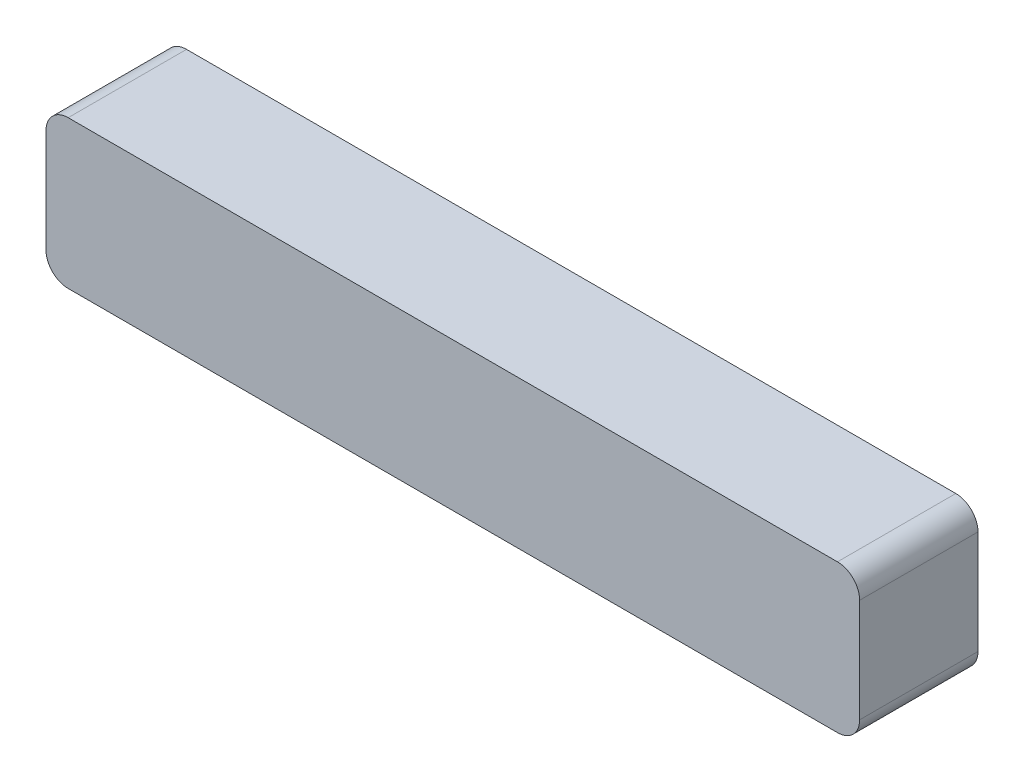
SolidWorks part; units mm, degrees
ref_plane "前视基准面" through (0, 0, 0) normal (0, 0, 1) x (1, 0, 0)
ref_plane "上视基准面" through (0, 0, 0) normal (0, 1, 0) x (1, 0, 0)
ref_plane "右视基准面" through (0, 0, 0) normal (1, 0, 0) x (0, 0, -1)
sketch "草图1" plane through (0, 0, 0) normal (0, 0, 1) x (1, 0, 0)
  line L1 (3, 0) -> (107, 0)
  line L2 (0, 3) -> (0, 17)
  line L3 (3, 20) -> (107, 20)
  line L4 (110, 3) -> (110, 17)
  arc A0 (110, 3) -> (107, 0) centre (107, 3) cw
  arc A1 (110, 17) -> (107, 20) centre (107, 17) ccw
  arc A2 (0, 3) -> (3, 0) centre (3, 3) ccw
  arc A3 (0, 17) -> (3, 20) centre (3, 17) cw
  point P7 (110, 0)
  point P12 (0, 0)
  point P15 (0, 20)
  dimension "D3" = 3
  dimension "D1" = 20
  dimension "D2" = 110
extrude "凸台-拉伸1" add sketch "草图1" along normal blind 16
